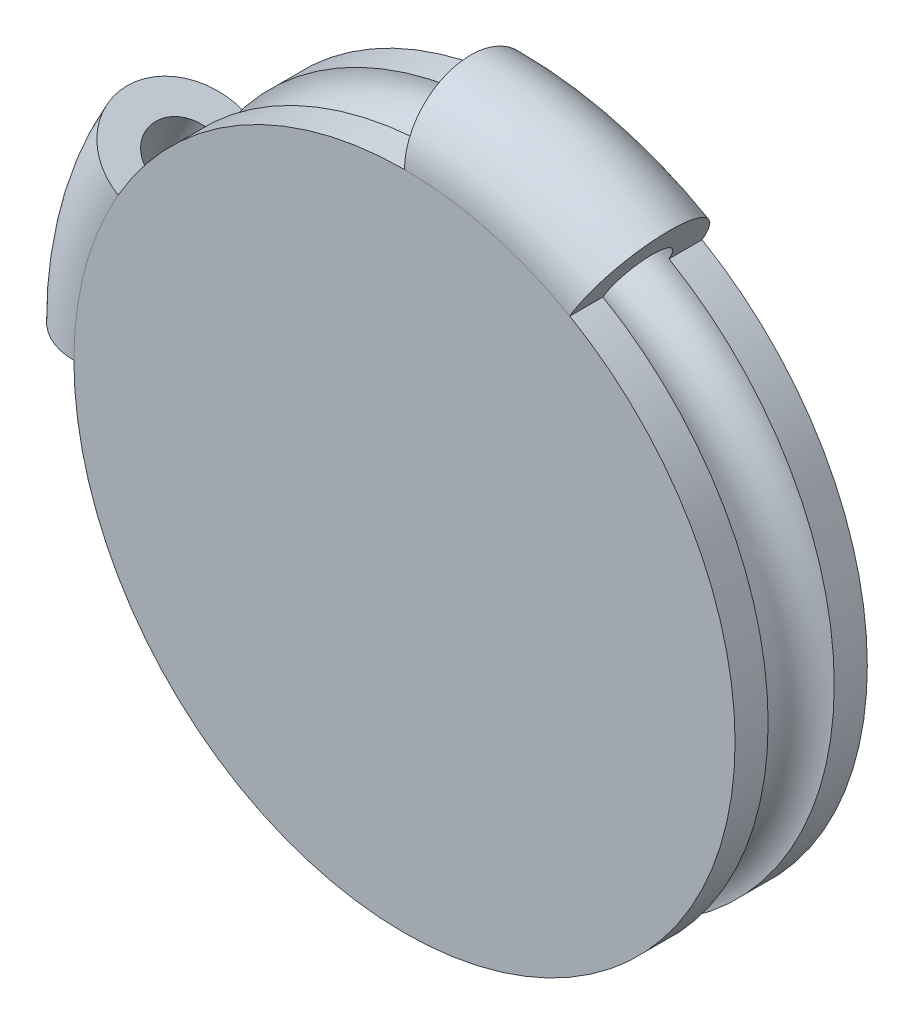
SolidWorks part; units mm, degrees
ref_plane "Plan de face" through (0, 0, 0) normal (0, 0, 1) x (1, 0, 0)
ref_plane "Plan de dessus" through (0, 0, 0) normal (0, 1, 0) x (1, 0, 0)
ref_plane "Plan de droite" through (0, 0, 0) normal (1, 0, 0) x (0, 0, -1)
sketch "Esquisse1" plane through (0, 0, 0) normal (0, 0, 1) x (1, 0, 0)
  circle A0 centre (0, 0) radius 10
  dimension "D1" = 20
extrude "Boss.-Extru.1" add sketch "Esquisse1" along normal mid plane 4
sketch "Esquisse4" plane through (0, 0, 0) normal (0, 1, 0) x (1, 0, 0)
  line L0 (-10, 2) -> (-10, -2) construction
  line L1 (0, -2) -> (0, 2) construction
  line L2 (-10, -2) -> (10, -2) construction
  line L3 (10, 2) -> (-10, 2) construction
  circle A0 centre (-10, 0) radius 2
revolve "Révolution1" add sketch "Esquisse4" angle 120 about L1
sketch "Esquisse2" plane through (0, 0, 0) normal (1, 0, 0) x (0, 0, -1)
  line L1 (8.6344, 0) -> (0, 0) construction
  circle A1 centre (0, 10) radius 1
  dimension "D1" = 2
  dimension "D2" = 10
revolve "Enlèvement de matière-Révolution1" cut sketch "Esquisse2" angle 360 about L1
sketch "Esquisse6" plane through (0, 0, 0) normal (1, 0, 0) x (0, 0, -1)
  line L0 (0, 0) -> (7.2494, 0) construction
  line L1 (-2, 10) -> (-1, 10)
  line L2 (1, 10) -> (2, 10)
  arc A0 (2, 10) -> (-2, 10) centre (0, 10) ccw
  arc A1 (1, 10) -> (-1, 10) centre (0, 10) ccw
  dimension "D2" = 4
  dimension "D3" = 2
  dimension "D1" = 10
revolve "Enlèvement de matière-Révolution2" cut sketch "Esquisse6" angle 60 about L0
